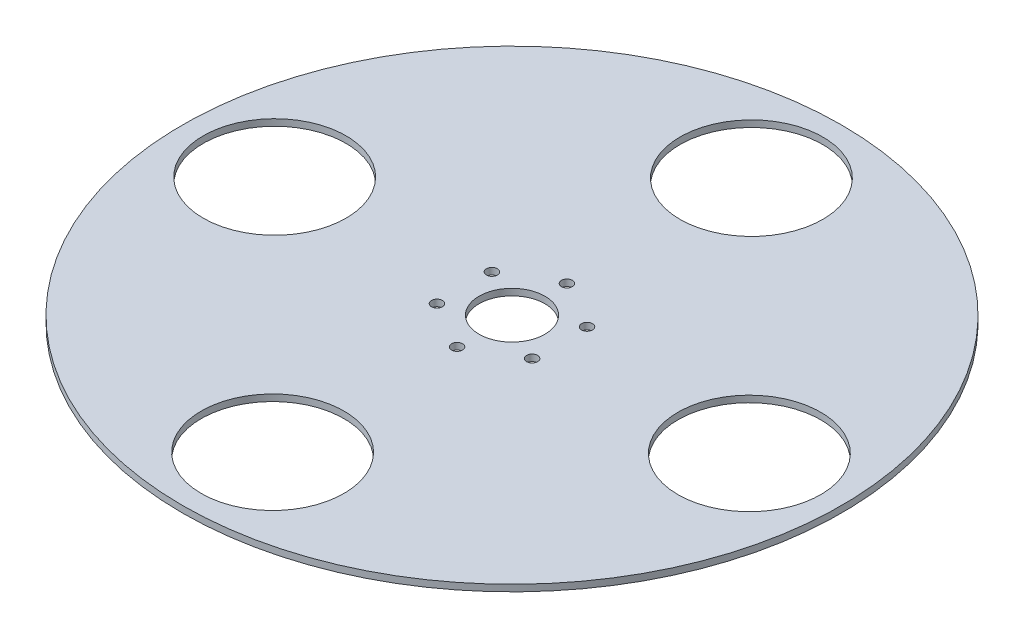
SolidWorks part; units mm, degrees
ref_plane "Front Plane" through (0, 0, 0) normal (0, 0, 1) x (1, 0, 0)
ref_plane "Top Plane" through (0, 0, 0) normal (0, 1, 0) x (1, 0, 0)
ref_plane "Right Plane" through (0, 0, 0) normal (1, 0, 0) x (0, 0, -1)
sketch "Sketch1" plane through (0, 0, 0) normal (0, 1, 0) x (1, 0, 0)
  circle A0 centre (0, 0) radius 150
  circle A1 centre (0, 0) radius 15
  circle A2 centre (0, 25) radius 2.5
  circle A3 centre (21.6506, 12.5) radius 2.5
  circle A4 centre (21.6506, -12.5) radius 2.5
  circle A5 centre (0, -25) radius 2.5
  circle A6 centre (-21.6506, -12.5) radius 2.5
  circle A7 centre (-21.6506, 12.5) radius 2.5
  circle A8 centre (0.4687, 108.499) radius 32.5
  circle A9 centre (108.499, -0.4687) radius 32.5
  circle A10 centre (-0.4687, -108.499) radius 32.5
  circle A11 centre (-108.499, 0.4687) radius 32.5
  point P8 (0, 0)
  dimension "D1" = 300
  dimension "D2" = 30
  dimension "D3" = 5
  dimension "D6" = 65
  dimension "D4" = 25
  dimension "D7" = 108.5
  dimension "D5" = 6
  dimension "D8" = 4
extrude "Boss-Extrude1" add sketch "Sketch1" along normal blind 3
